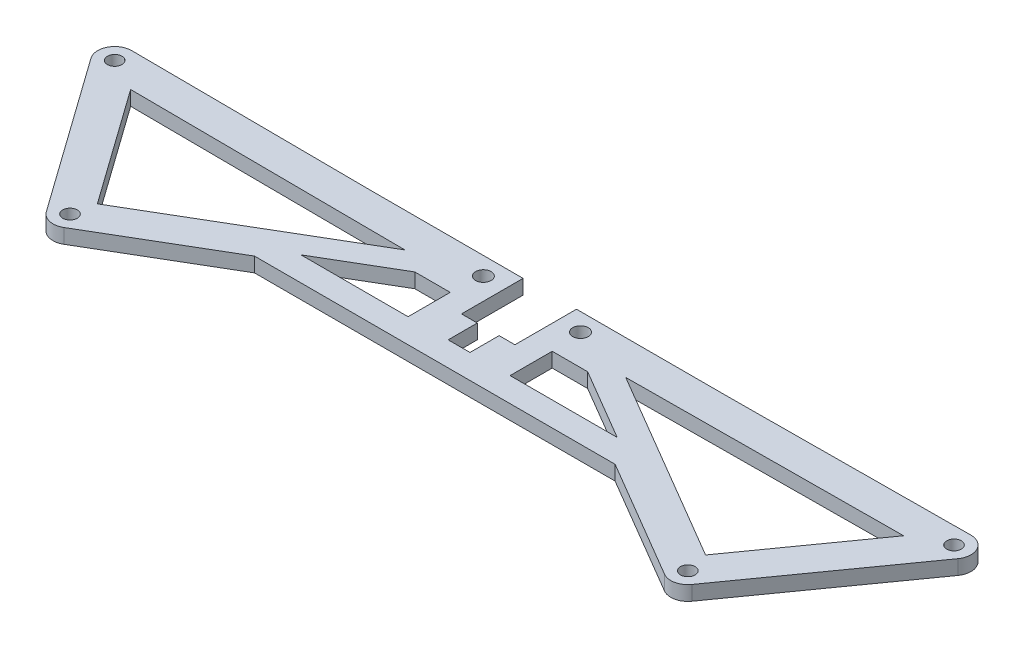
SolidWorks part; units mm, degrees
material "Thornel Mat VMA"
ref_plane "前视基准面" through (0, 0, 0) normal (0, 0, 1) x (1, 0, 0)
ref_plane "上视基准面" through (0, 0, 0) normal (0, 1, 0) x (1, 0, 0)
ref_plane "右视基准面" through (0, 0, 0) normal (1, 0, 0) x (0, 0, -1)
sketch "草图1" plane through (0, 0, 0) normal (0, 1, 0) x (1, 0, 0)
  line L1 (-91, -20) -> (91, -20)
  line L2 (-91, -20) -> (-91, 20)
  line L3 (-91, 20) -> (91, 20)
  line L4 (91, -20) -> (91, 20)
  line L5 (-91, -20) -> (91, 20) construction
  line L6 (-91, 20) -> (91, -20) construction
  point P0 (0, 0)
  dimension "D1" = 40
  dimension "D2" = 182
extrude "凸台-拉伸1" add sketch "草图1" along normal mid plane 3
sketch "草图2" plane through (0, 1.5, 0) normal (0, 1, 0) x (1, 0, 0)
  line L0 (0, 46.376) -> (0, -27.2124) construction
  line L1 (-91, -20) -> (91, -20) construction
  circle A0 centre (-86.4, 15.5) radius 1.5
  circle A1 centre (-63.6, -16.5) radius 1.5
  circle A2 centre (63.6, -16.5) radius 1.5
  circle A3 centre (86.4, 15.5) radius 1.5
  dimension "D1" = 3
  dimension "D2" = 32
  dimension "D3" = 22.8
  dimension "D5" = 3.5
  dimension "D4" = 127.2
extrude "切除-拉伸1" cut sketch "草图2" against normal through all
sketch "草图3" plane through (0, 1.5, 0) normal (0, 1, 0) x (1, 0, 0)
  line L0 (0, 70.567) -> (0, -65.4722) construction
  line L1 (5.5, 20) -> (-5.5, 20)
  line L2 (91, 20) -> (-91, 20) construction
  line L3 (-5.5, 20) -> (-5.5, 6)
  line L4 (-5.5, 6) -> (-2.25, 6)
  line L5 (-2.25, 6) -> (-2.25, 0)
  line L6 (-2.25, 0) -> (2.25, 0)
  line L7 (2.25, 6) -> (2.25, 0)
  line L8 (5.5, 6) -> (2.25, 6)
  line L9 (5.5, 20) -> (5.5, 6)
  circle A2 centre (-10, 15) radius 1.6
  circle A3 centre (10, 15) radius 1.6
  point P12 (0, 0)
  point P15 (0, 20)
  dimension "D4" = 3.2
  dimension "D5" = 20
  dimension "D6" = 5
  dimension "D1" = 11
  dimension "D2" = 6
  dimension "D3" = 4.5
extrude "切除-拉伸2" cut sketch "草图3" against normal through all
sketch "草图4" plane through (0, 1.5, 0) normal (0, 1, 0) x (1, 0, 0)
  line L0 (-86.4, 15.5) -> (-63.6, -16.5) construction
  line L1 (-83.5495, 17.531) -> (-60.7495, -14.469)
  line L2 (-89.2505, 13.469) -> (-66.4505, -18.531)
  line L3 (-63.6, -16.5) -> (-10, 15) construction
  line L4 (-65.3733, -13.4825) -> (-11.7733, 18.0175)
  line L5 (-61.8267, -19.5175) -> (-8.2267, 11.9825)
  line L6 (-86.4, 15.5) -> (-10, 15) construction
  line L7 (-86.3771, 18.9999) -> (-9.9771, 18.4999)
  line L8 (-86.4229, 12.0001) -> (-10.0229, 11.5001)
  line L9 (10, 15) -> (63.6, -16.5) construction
  line L10 (11.7733, 18.0175) -> (65.3733, -13.4825)
  line L11 (8.2267, 11.9825) -> (61.8267, -19.5175)
  line L12 (63.6, -16.5) -> (86.4, 15.5) construction
  line L13 (60.7495, -14.469) -> (83.5495, 17.531)
  line L14 (66.4505, -18.531) -> (89.2505, 13.469)
  line L15 (86.4, 15.5) -> (10, 15) construction
  line L16 (86.4229, 12.0001) -> (10.0229, 11.5001)
  line L17 (86.3771, 18.9999) -> (9.9771, 18.4999)
  line L19 (-37.1239, -5) -> (37.1239, -5)
  line L20 (-37.1239, -5) -> (-37.1239, 18.6776)
  line L21 (-37.1239, 18.6776) -> (37.1239, 18.6776)
  line L22 (37.1239, -5) -> (37.1239, 18.6776)
  line L23 (-37.1239, -5) -> (37.1239, 18.6776) construction
  line L24 (-37.1239, 18.6776) -> (37.1239, -5) construction
  arc A0 (-83.5495, 17.531) -> (-89.2505, 13.469) centre (-86.4, 15.5) ccw
  arc A1 (-66.4505, -18.531) -> (-60.7495, -14.469) centre (-63.6, -16.5) ccw
  arc A2 (-65.3733, -13.4825) -> (-61.8267, -19.5175) centre (-63.6, -16.5) ccw
  arc A3 (-8.2267, 11.9825) -> (-11.7733, 18.0175) centre (-10, 15) ccw
  arc A4 (-86.3771, 18.9999) -> (-86.4229, 12.0001) centre (-86.4, 15.5) ccw
  arc A5 (-10.0229, 11.5001) -> (-9.9771, 18.4999) centre (-10, 15) ccw
  arc A6 (11.7733, 18.0175) -> (8.2267, 11.9825) centre (10, 15) ccw
  arc A7 (61.8267, -19.5175) -> (65.3733, -13.4825) centre (63.6, -16.5) ccw
  arc A8 (60.7495, -14.469) -> (66.4505, -18.531) centre (63.6, -16.5) ccw
  arc A9 (89.2505, 13.469) -> (83.5495, 17.531) centre (86.4, 15.5) ccw
  arc A10 (86.4229, 12.0001) -> (86.3771, 18.9999) centre (86.4, 15.5) ccw
  arc A11 (9.9771, 18.4999) -> (10.0229, 11.5001) centre (10, 15) ccw
  point P4 (-75, -0.5)
  point P9 (-36.8, -0.75)
  point P17 (-48.2, 15.25)
  point P24 (36.8, -0.75)
  point P33 (75, -0.5)
  point P41 (48.2, 15.25)
  point P48 (0, 6.8388)
  line M8 (-5.5, 6) -> (-5.5, 20)
  line M9 (-5.5, 20) -> (-91, 20)
  line M10 (-91, 20) -> (-91, -20)
  line M11 (-91, -20) -> (91, -20)
  line M12 (91, -20) -> (91, 20)
  line M13 (91, 20) -> (5.5, 20)
  line M14 (5.5, 20) -> (5.5, 6)
  dimension "D1" = 7
  dimension "D2" = 5
extrude "切除-拉伸3" cut sketch "草图4" against normal through all contours A3 L21 A1 L2 A0 L7 M8 M9 M10 M11 | L4 L20 L8 L1 | L20 L4 L8 | A7 L11 L19 L5 A1 M11 | L22 L10 L13 L16 | L10 L22 L16 | A9 L14 A7 L21 A6 L17 M11 M12 M13 M14
sketch "草图5" plane through (0, 1.5, 0) normal (0, 1, 0) x (1, 0, 0)
  line L0 (-17.7976, 8.6776) -> (-32.5633, 0)
  line L1 (-32.5633, 0) -> (-10.5, 0)
  line L2 (-10.5, 0) -> (-10.5, 8.6776)
  line L3 (-17.7976, 8.6776) -> (-10.5, 8.6776)
  line L4 (-62.6097, -11.8583) -> (-22.7219, 11.5832) construction
  line L5 (-37.1239, -5) -> (37.1239, -5) construction
  line L6 (-5.5, 18.6776) -> (-5.5, 6) construction
  line L8 (-37.1239, 18.6776) -> (-5.5, 18.6776) construction
  line L9 (0, 26.5115) -> (0, -20.7718) construction
  line L10 (17.7976, 8.6776) -> (10.5, 8.6776)
  line L11 (10.5, 0) -> (10.5, 8.6776)
  line L12 (32.5633, 0) -> (10.5, 0)
  line L13 (17.7976, 8.6776) -> (32.5633, 0)
  dimension "D1" = 5
  dimension "D2" = 5
  dimension "D3" = 5
  dimension "D4" = 10
extrude "切除-拉伸4" cut sketch "草图5" against normal through all
